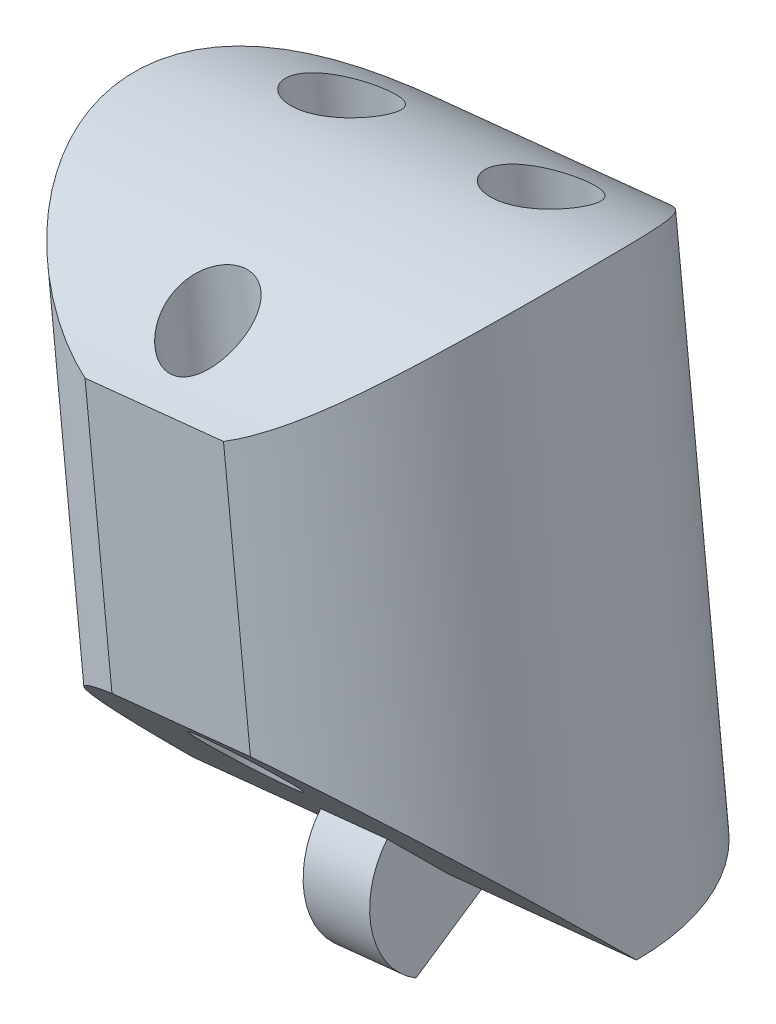
SolidWorks part; units mm, degrees
ref_plane "Front Plane" through (0, 0, 0) normal (0, 0, 1) x (1, 0, 0)
ref_plane "Top Plane" through (0, 0, 0) normal (0, 1, 0) x (1, 0, 0)
ref_plane "Right Plane" through (0, 0, 0) normal (1, 0, 0) x (0, 0, -1)
sketch "Sketch2" plane through (0, 0, 0) normal (0, 0, 1) x (1, 0, 0)
  line L0 (0, 0) -> (90, 0)
  line L1 (90, 0) -> (90, 120)
  line L2 (90, 120) -> (0, 120)
  line L3 (0, 120) -> (0, 0)
  line L4 (0, 120) -> (-10, 120)
  line L5 (-10, 120) -> (-10, 16.9491)
  line L6 (-10, 120) -> (57.5, 127)
  line L7 (57.5, 127) -> (90, 124)
  line L8 (90, 120) -> (99, 60)
  line L10 (90, 124) -> (90, 120)
  line L11 (5.9147, 0) -> (5.9147, -25)
  line L12 (5.9147, -25) -> (-4.0853, -25)
  line L13 (-4.0853, -29) -> (-4.0853, 0)
  line L14 (80, 0) -> (80, -25)
  line L15 (80, -25) -> (90, -25)
  line L16 (90, -29) -> (90, 0)
  line L17 (15.7927, 122.6748) -> (5.4776, 222.1414)
  line L18 (5.4776, 222.1414) -> (21.3923, 223.7918)
  line L19 (21.3923, 223.7918) -> (31.7073, 124.3252)
  line L20 (7.6492, 201.201) -> (23.5639, 202.8514)
  line L21 (10.9066, 169.7905) -> (26.8212, 171.441)
  line L22 (-10, 120) -> (-20.0396, 216.8108)
  line L23 (-20.0396, 216.8108) -> (-4.125, 218.4612)
  line L24 (-4.125, 218.4612) -> (5.9147, 121.6504)
  line L25 (-17.926, 196.4296) -> (-2.0114, 198.08)
  line L26 (-14.7556, 165.8578) -> (1.159, 167.5082)
  line L27 (57.5, 127) -> (46.9095, 229.1223)
  line L28 (46.9095, 229.1223) -> (30.9949, 227.4719)
  line L29 (30.9949, 227.4719) -> (41.5853, 125.3496)
  line L30 (33.2245, 205.9725) -> (49.1391, 207.6229)
  line L31 (36.5688, 173.7233) -> (52.4835, 175.3737)
  line L34 (90, 124) -> (99.1917, 223.5767)
  line L35 (99.1917, 223.5767) -> (83.2594, 225.0473)
  line L36 (83.2594, 225.0473) -> (74.0677, 125.4707)
  line L38 (81.3243, 204.0838) -> (97.2566, 202.6132)
  line L39 (78.4217, 172.6386) -> (94.354, 171.1679)
  line L40 (62.4078, 79.6749) -> (57.5, 127) construction
  line L41 (41.5853, 125.3496) -> (46.4931, 78.0244) construction
  line L42 (46.4931, 78.0244) -> (62.4078, 79.6749) construction
  line L43 (31.7073, 124.3252) -> (36.6151, 77.0001) construction
  line L44 (36.6151, 77.0001) -> (20.7005, 75.3496) construction
  line L45 (20.7005, 75.3496) -> (15.7927, 122.6748) construction
  line L46 (5.9147, 121.6504) -> (10.8224, 74.3253) construction
  line L47 (10.8224, 74.3253) -> (-5.0922, 72.6749) construction
  line L48 (-5.0922, 72.6749) -> (-10, 120) construction
  line L49 (74.0677, 125.4707) -> (69.6944, 78.0931) construction
  line L50 (69.6944, 78.0931) -> (85.7624, 78.0931) construction
  line L51 (85.7624, 78.0931) -> (90, 124) construction
  line L52 (-12.0823, 217.636) -> (10.4873, 0) construction
  line L53 (13.4349, 222.9666) -> (36.5574, 0) construction
  line L54 (38.9522, 228.2971) -> (62.6275, 0) construction
  line L55 (91.2256, 224.312) -> (70.5198, 0) construction
  line L59 (99, 60) -> (93.5277, 44.9649)
  line L60 (99, 60) -> (169.4769, 34.3485)
  line L61 (169.4769, 34.3485) -> (164.0046, 19.3134)
  line L62 (164.0046, 19.3134) -> (93.5277, 44.9649)
  line L63 (90, -2) -> (100, -2)
  line L64 (141.2862, 44.6091) -> (135.8138, 29.574)
  line L65 (99, 60) -> (55.7741, 75.7329) construction
  line L66 (55.7741, 75.7329) -> (50.3018, 60.6978) construction
  line L67 (100, -2) -> (100, -29)
  line L70 (-4.0853, -2) -> (-14.0853, -2)
  line L71 (-14.0853, -2) -> (-14.0853, -29)
  line L74 (-4.0853, 0) -> (0, 0)
  line L75 (-14.0853, -29) -> (-14.0853, -112.587)
  line L76 (-14.0853, -112.587) -> (100, -112.587)
  line L77 (100, -112.587) -> (100, -29)
  line L78 (-14.0853, -29) -> (100, -29)
  line L79 (-14.0853, -14.5) -> (100, -14.5) construction
  line L80 (31.7073, -112.587) -> (31.7073, -122.6232)
  line L81 (31.7073, -122.6232) -> (42.9573, -122.6232)
  line L82 (42.9573, -122.6232) -> (42.9573, -112.587)
  line L83 (-14.0853, -112.587) -> (-88.3667, -112.587)
  line L84 (-88.3667, -112.587) -> (-88.3667, -128.2699)
  line L85 (-88.3667, -128.2699) -> (169.4958, -128.2699)
  line L86 (169.4958, -128.2699) -> (169.4958, -112.587)
  line L87 (169.4958, -112.587) -> (100, -112.587)
  line L88 (90, 60) -> (-10, 60) construction
  line L89 (50.3018, 60.6978) -> (93.5277, 44.9649) construction
  line L90 (87.2806, 55.7521) -> (166.7408, 26.8309) construction
  line L91 (87.2806, 55.7521) -> (82.1749, 52.5336) construction
  line L92 (82.1749, 52.5336) -> (77.3257, 0) construction
  line L93 (83.1185, 56.6957) -> (86.337, 51.59) construction
  arc A0 (-10, 16.9491) -> (-4.0853, 0) centre (14.9876, 16.1624) ccw
  arc A1 (93.5277, 44.9649) -> (90, 0) centre (-126.4069, 39.5988) cw
  point P42 (41.1818, 206.7977)
  point P100 (84.7278, 54.1428)
  point P101 (84.7278, 54.1428)
  dimension "D11" = 47.3684
  dimension "D35" = 9
  dimension "D32" = 220
  dimension "D36" = 25
  dimension "D1" = 120
  dimension "D2" = 90
  dimension "D3" = 10
  dimension "D5" = 67.862
  dimension "D6" = 7
  dimension "D7" = 4
  dimension "D8" = 16
  dimension "D9" = 16
  dimension "D10" = 100
  dimension "D12" = 31.5789
  dimension "D13" = 16
  dimension "D14" = 16
  dimension "D15" = 16
  dimension "D16" = 25.7927
  dimension "D17" = 100
  dimension "D18" = 21.0526
  dimension "D19" = 31.5789
  dimension "D20" = 97.33
  dimension "D21" = 102.67
  dimension "D22" = 20.4905
  dimension "D23" = 30.7358
  dimension "D24" = 21.6147
  dimension "D25" = 32.4221
  dimension "D26" = 25
  dimension "D28" = 25
  dimension "D29" = 75
  dimension "D30" = 47.5789
  dimension "D31" = 30
  dimension "D33" = 46
  dimension "D34" = 20
  dimension "D37" = 2
  dimension "D38" = 2
  dimension "D39" = 27
  dimension "D40" = 10
  dimension "D41" = 10
  dimension "D42" = 27
  dimension "D43" = 14.5
  dimension "D44" = 127.5
ref_plane "Plane1" through (87.2806, 55.7521, 0) normal (-0.846, -0.5333, 0) x (0, 0, 1)
ref_plane "Plane2" through (82.1749, 52.5336, 0) normal (-0.0919, -0.9958, 0) x (-0.9958, 0.0919, 0)
ref_plane "Plane3" through (91.2256, 224.312, 0) normal (-0.0919, -0.9958, 0) x (-0.9958, 0.0919, 0)
ref_plane "Plane4" through (38.9522, 228.2971, 0) normal (0.1032, -0.9947, 0) x (-0.9947, -0.1032, 0)
ref_plane "Plane5" through (13.4349, 222.9666, 0) normal (0.1032, -0.9947, 0) x (-0.9947, -0.1032, 0)
ref_plane "Plane7" through (166.7408, 26.8309, 0) normal (0.9397, -0.342, 0) x (0, 0, -1)
ref_plane "Plane8" through (110.4217, -40.1902, 0) normal (0.9397, -0.342, 0) x (0, 0, -1)
ref_plane "Plane9" through (19.3664, 209.803, 0) normal (-0.0919, -0.9958, 0) x (-0.9958, 0.0919, 0)
ref_plane "Plane10" through (16.4638, 178.3578, 0) normal (-0.0919, -0.9958, 0) x (-0.9958, 0.0919, 0)
ref_plane "Plane11" through (-20.7793, 200.3721, 0) normal (0.1032, -0.9947, 0) x (-0.9947, -0.1032, 0)
ref_plane "Plane12" through (-17.435, 168.1229, 0) normal (0.1032, -0.9947, 0) x (-0.9947, -0.1032, 0)
ref_plane "Plane13" through (-20.5619, 198.2754, 0) normal (0.1032, -0.9947, 0) x (-0.9947, -0.1032, 0)
ref_plane "Plane14" through (-17.3045, 166.8649, 0) normal (0.1032, -0.9947, 0) x (-0.9947, -0.1032, 0)
ref_plane "Plane15" through (-12.0823, 217.636, 0) normal (0.1032, -0.9947, 0) x (-0.9947, -0.1032, 0)
ref_plane "Plane16" through (-20.3445, 196.1788, 0) normal (0.1032, -0.9947, 0) x (-0.9947, -0.1032, 0)
ref_plane "Plane17" through (-17.1741, 165.607, 0) normal (0.1032, -0.9947, 0) x (-0.9947, -0.1032, 0)
ref_plane "Plane18" through (12.1098, 131.1899, 0) normal (-0.0919, -0.9958, 0) x (-0.9958, 0.0919, 0)
ref_plane "Plane19" through (-12.4184, 119.7492, 0) normal (0.1032, -0.9947, 0) x (-0.9947, -0.1032, 0)
ref_plane "Plane20" through (0, 0, 0) normal (0, 0, 1) x (0.1032, -0.9947, 0)
ref_plane "Plane21" through (0, 0, 0) normal (0, 0, 1) x (-0.0919, -0.9958, 0)
ref_plane "Plane22" through (10.3758, 1.076, 0) normal (-0.9947, -0.1032, 0) x (0.1032, -0.9947, 0)
ref_plane "Plane23" through (36.1684, 3.7508, 0) normal (-0.9947, -0.1032, 0) x (0.1032, -0.9947, 0)
ref_plane "Plane24" through (61.9611, 6.4256, 0) normal (-0.9947, -0.1032, 0) x (0.1032, -0.9947, 0)
ref_plane "Plane25" through (69.924, -6.4545, 0) normal (-0.9958, 0.0919, 0) x (-0.0919, -0.9958, 0)
sketch "Sketch3" plane through (-12.0823, 217.636, 0) normal (0.1032, -0.9947, 0) x (-0.9947, -0.1032, 0)
  circle A0 centre (0, 0) radius 8
  dimension "D1" = 16
extrude "Boss-Extrude1" add sketch "Sketch3" along normal blind 20.4905
sketch "Sketch4" plane through (10.3758, 1.076, 0) normal (-0.9947, -0.1032, 0) x (0.1032, -0.9947, 0)
  line L0 (-217.7214, 8) -> (-213.7214, 8)
  line L1 (-197.2309, 8) -> (-217.7214, 8) construction
  line L2 (-217.7214, 8) -> (-217.7214, -8)
  line L3 (-217.7214, -8) -> (-213.7214, -8)
  line L4 (-217.7214, -8) -> (-197.2309, -8) construction
  arc A0 (-213.7214, 8) -> (-213.7214, -8) centre (-207.3937, 0) ccw
  dimension "D2" = 10.2
  dimension "D1" = 4
extrude "Cut-Extrude1" cut sketch "Sketch4" against normal through all and the other way through all
sketch "Sketch5" plane through (10.3758, 1.076, 0) normal (-0.9947, -0.1032, 0) x (0.1032, -0.9947, 0)
  line L0 (-197.2309, 0) -> (-205.2309, 8)
  line L1 (-197.2309, -8) -> (-197.2309, 8) construction
  line L2 (-197.2309, 8) -> (-213.7214, 8) construction
  line L3 (-205.2309, 8) -> (-197.2309, 8)
  line L4 (-197.2309, 8) -> (-197.2309, 0)
  dimension "D1" = 45
extrude "Cut-Extrude2" cut sketch "Sketch5" against normal through all and the other way through all
sketch "Sketch7" plane through (10.3758, 1.076, 0) normal (-0.9947, -0.1032, 0) x (0.1032, -0.9947, 0)
  line L11 (-199.2108, 1.9799) -> (-197.2309, 0)
  line L14 (-197.2309, 0) -> (-197.2309, -2.8)
  line L15 (-197.2309, -2.8) -> (-194.806, 1.4)
  line L16 (-197.2309, 0) -> (-205.2309, 8) construction
  arc A0 (-199.2108, 1.9799) -> (-194.806, 1.4) centre (-197.2309, 0) cw
  dimension "D2" = 2.8
  dimension "D1" = 30
  dimension "D3" = 2.8
extrude "Boss-Extrude3" add sketch "Sketch7" along normal mid plane 2.4
sketch "Sketch8" plane through (-12.0823, 217.636, 0) normal (0.1032, -0.9947, 0) x (-0.9947, -0.1032, 0)
  line L0 (8, 0) -> (-8, 0) construction
  circle A0 centre (-3.6, 3) radius 1.6
  circle A1 centre (3.6, 3) radius 1.6
  circle A3 centre (0, -5.5) radius 1.4
  point P6 (0, 0)
  dimension "D1" = 3.2
  dimension "D2" = 3.2
  dimension "D7" = 2.8
  dimension "D3" = 3
  dimension "D4" = 3
  dimension "D5" = 3.6
  dimension "D6" = 3.6
  dimension "D8" = 5.5
extrude "Cut-Extrude3" cut sketch "Sketch8" against normal through all and the other way through all
sketch "Sketch9" plane through (-20.3445, 196.1788, 0) normal (0.1032, -0.9947, 0) x (0.9947, 0.1032, 0)
  line L0 (7.9334, -7.6) -> (12.9294, -7.6)
  line L1 (2.4314, 0) -> (18.4314, 0) construction
  line L2 (7.9334, 7.6) -> (12.9294, 7.6)
  arc A0 (2.4314, 0) -> (18.4314, 0) centre (10.4314, 0) ccw construction
  arc A1 (7.9334, -7.6) -> (12.9294, -7.6) centre (10.4314, 0) ccw
  arc A2 (18.4314, 0) -> (2.4314, 0) centre (10.4314, 0) ccw construction
  arc A3 (7.9334, 7.6) -> (12.9294, 7.6) centre (10.4314, 0) cw
  point P14 (10.4314, 7.6)
  dimension "D1" = 7.6
  dimension "D2" = 7.6
extrude "Cut-Extrude4" cut sketch "Sketch9" against normal through all
